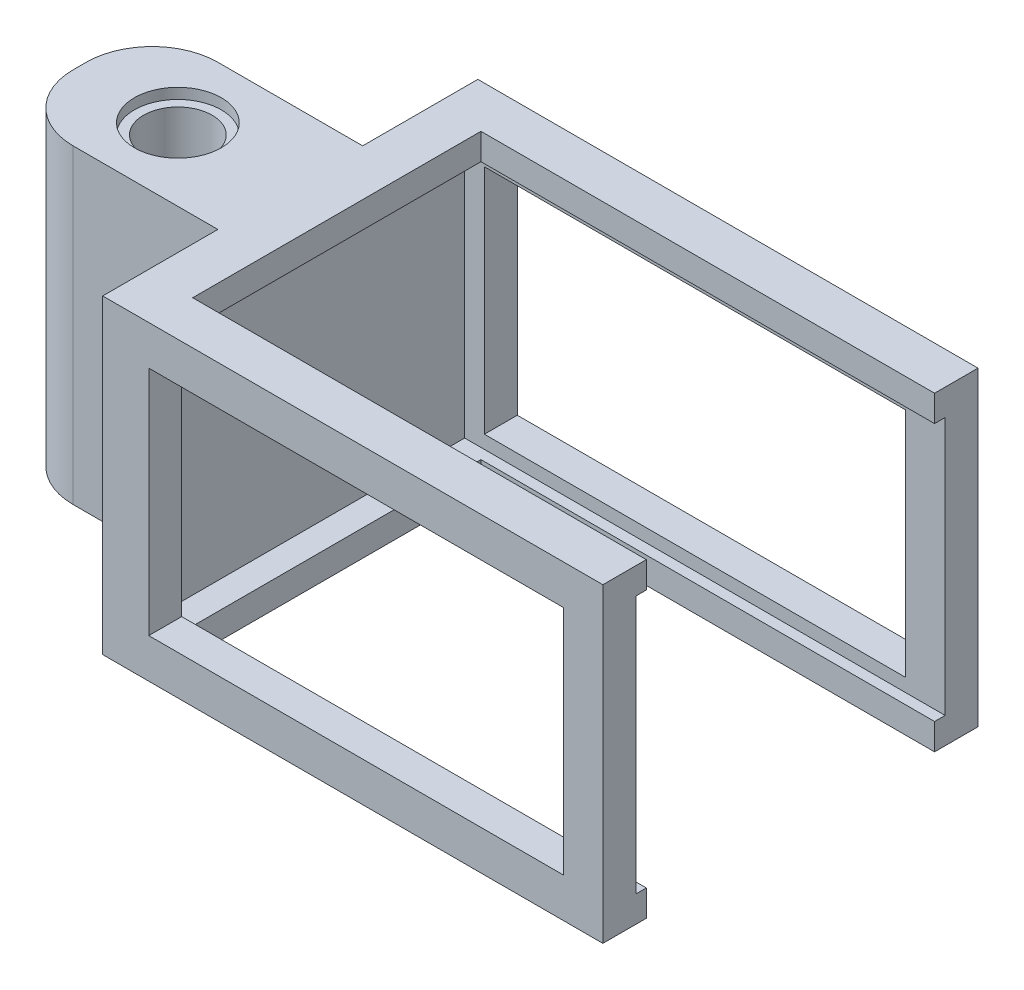
SolidWorks part; units mm, degrees
ref_plane "Front Plane" through (0, 0, 0) normal (0, 0, 1) x (1, 0, 0)
ref_plane "Top Plane" through (0, 0, 0) normal (0, 1, 0) x (1, 0, 0)
ref_plane "Right Plane" through (0, 0, 0) normal (1, 0, 0) x (0, 0, -1)
sketch "Sketch2" plane through (0, 0, 0) normal (0, 0, 1) x (1, 0, 0)
  line L1 (0, 0) -> (38, 0)
  line L2 (0, 0) -> (0, 23.6)
  line L3 (0, 23.6) -> (38, 23.6)
  line L4 (38, 0) -> (38, 23.6)
  dimension "D1" = 23.6
  dimension "D2" = 38
extrude "Boss-Extrude2" add sketch "Sketch2" along normal blind 2.5
sketch "Sketch3" plane through (0, 0, 2.5) normal (0, 0, 1) x (1, 0, 0)
  line L0 (38, 23.6) -> (38, 20.6) construction
  line L1 (38, 0) -> (38, 23.6) construction
  line L2 (38, 0) -> (38, 3) construction
  line L3 (0, 11.8) -> (3, 11.8) construction
  line L4 (0, 23.6) -> (0, 0) construction
  line L6 (38, 20.6) -> (3, 20.6)
  line L7 (38, 20.6) -> (38, 3)
  line L8 (38, 3) -> (3, 3)
  line L9 (3, 20.6) -> (3, 3)
  dimension "D1" = 3
  dimension "D2" = 3
  dimension "D3" = 3
extrude "Cut-Extrude2" cut sketch "Sketch3" against normal blind 2.5
sketch "Sketch5" plane through (0, 0, 2.5) normal (0, 0, 1) x (1, 0, 0)
  line L0 (38, 20.6) -> (38, 23.6) construction
  line L1 (0, 23.6) -> (38, 23.6)
  line L2 (0, 23.6) -> (0, 21.6)
  line L3 (0, 21.6) -> (38, 21.6)
  line L4 (38, 23.6) -> (38, 21.6)
  line L5 (0, 23.6) -> (0, 0) construction
  line L6 (38, 0) -> (0, 0)
  line L7 (38, 0) -> (38, 2)
  line L8 (38, 2) -> (0, 2)
  line L9 (0, 0) -> (0, 2)
  line L10 (0, 0) -> (1.5, 0) construction
  line L11 (0, 0) -> (1.5, 0)
  line L12 (0, 0) -> (0, 23.6)
  line L13 (0, 23.6) -> (1.5, 23.6)
  line L14 (1.5, 0) -> (1.5, 23.6)
  line L15 (0, 11.8) -> (1.5, 11.8) construction
  line M4 (38, 0) -> (38, 3)
  line M8 (38, 20.6) -> (38, 23.6)
  line M9 (38, 23.6) -> (0, 23.6)
  line M10 (0, 23.6) -> (0, 0)
  line M11 (0, 0) -> (38, 0)
  dimension "D1" = 2
  dimension "D2" = 2
  dimension "D3" = 1.5
extrude "Boss-Extrude3" add sketch "Sketch5" along normal blind 26 contours L14 L3 M8 M9 | L3 L14 L1 M10 | L8 L14 L3 M10 | L14 L8 M11 M10 | L14 L6 L8 M4
sketch "Sketch7" plane through (0, 2, 0) normal (0, 1, 0) x (1, 0, 0)
  line L0 (1.5, -28.5) -> (1.5, -2.5) construction
  line L1 (38, -28.5) -> (1.5, -28.5)
  line L2 (38, -28.5) -> (38, -26)
  line L3 (38, -26) -> (1.5, -26)
  line L4 (1.5, -28.5) -> (1.5, -26)
  dimension "D1" = 2.5
extrude "Boss-Extrude5" add sketch "Sketch7" along normal blind 1
sketch "Sketch10" plane through (0, 21.6, 0) normal (0, -1, 0) x (1, 0, 0)
  line L0 (38, 28.5) -> (38, 2.5) construction
  line L1 (1.5, 28.5) -> (38, 28.5)
  line L2 (1.5, 28.5) -> (1.5, 26)
  line L3 (1.5, 26) -> (38, 26)
  line L4 (38, 28.5) -> (38, 26)
  line L5 (25.4025, 26) -> (25.4025, 28.5)
  line M3 (38, 2.5) -> (38, 28.5)
  line M4 (38, 28.5) -> (1.5, 28.5)
  line M5 (1.5, 28.5) -> (1.5, 2.5)
  dimension "D1" = 2.5
extrude "Boss-Extrude6" add sketch "Sketch10" along normal blind 1 contours L5 L3 M3 M4 | L3 L5 L1 M5
sketch "Sketch11" plane through (1.5, 0, 0) normal (1, 0, 0) x (0, 0, -1)
  line L1 (-26, 3) -> (-28.5, 3)
  line L2 (-26, 3) -> (-26, 20.6)
  line L3 (-26, 20.6) -> (-28.5, 20.6)
  line L4 (-28.5, 3) -> (-28.5, 20.6)
extrude "Boss-Extrude7" add sketch "Sketch11" along normal blind 2
sketch "Sketch12" plane through (0, 21.6, 0) normal (0, -1, 0) x (-1, 0, 0)
  line L1 (12.2725, 16.9603) -> (-28.6118, 16.9603)
  line L2 (12.2725, 16.9603) -> (12.2725, 24.3169)
  line L3 (12.2725, 24.3169) -> (-28.6118, 24.3169)
  line L4 (-28.6118, 16.9603) -> (-28.6118, 24.3169)
ref_plane "Plane1" through (38, 21.6, 26) normal (0, 0, -1) x (-1, 0, 0)
sketch "Sketch15" plane through (0, 23.6, 0) normal (0, 1, 0) x (1, 0, 0)
  line L0 (34.1267, 0) -> (34.1267, -2.5) construction
  line L1 (38, 0) -> (0, 0) construction
  line L2 (34.5867, -28.5) -> (34.5867, -26) construction
  line L3 (38, -28.5) -> (0, -28.5) construction
  line L4 (44.4625, -26) -> (31.5375, -26) construction
  line L5 (0, -14.25) -> (3, -14.25) construction
  line L6 (0, -28.5) -> (0, 0) construction
  line L7 (38, -28.5) -> (38, 0) construction
  line L8 (34.1267, -2.5) -> (3.5372, -2.5)
  line L9 (34.1267, -2.5) -> (34.1267, -26)
  line L10 (34.1267, -26) -> (3.5372, -26)
  line L11 (3.5372, -2.5) -> (3.5372, -26)
  line L12 (3.5372, -2.5) -> (38, -2.5)
  line L13 (3.5372, -2.5) -> (3.5372, -26)
  line L14 (3.5372, -26) -> (38, -26)
  line L15 (38, -2.5) -> (38, -26)
  line M6 (38, -28.5) -> (38, 0)
  dimension "D1" = 2.5
  dimension "D2" = 3
extrude "Cut-Extrude4" cut sketch "Sketch15" against normal blind 30 contours L8 L11 L10 L9 | L9 L14 L12 M6
sketch "Sketch16" plane through (0, 3, 0) normal (0, 1, 0) x (1, 0, 0)
  line L0 (3, 0) -> (38, 0) construction
  line L1 (38, -2.5) -> (35, -2.5)
  line L2 (38, -2.5) -> (38, 0)
  line L3 (38, 0) -> (35, 0)
  line L4 (35, -2.5) -> (35, 0)
  dimension "D1" = 3
extrude "Boss-Extrude8" add sketch "Sketch16" along normal blind 20
sketch "Sketch17" plane through (0, 3, 0) normal (0, 1, 0) x (1, 0, 0)
  line L0 (38, -26) -> (3.5, -26) construction
  line L1 (38, -28.5) -> (35, -28.5)
  line L2 (38, -28.5) -> (38, -26)
  line L3 (38, -26) -> (35, -26)
  line L4 (35, -28.5) -> (35, -26)
  dimension "D1" = 3
extrude "Boss-Extrude9" add sketch "Sketch17" along normal blind 20
sketch "Sketch18" plane through (0, 23.6, 0) normal (0, 1, 0) x (1, 0, 0)
  line L0 (0, -14.25) -> (13.6, -14.25) construction
  line L1 (0, -28.5) -> (0, 0) construction
  circle A0 centre (13.6, -14.25) radius 3.69
  circle A1 centre (6.22, -14.25) radius 3.69
  circle A2 centre (-1.16, -14.25) radius 3.69
  circle A3 centre (-8.54, -14.25) radius 3.69
  dimension "D2" = 7.38
  dimension "D3" = 4
  dimension "D1" = 13.6
sketch "Sketch19" plane through (0, 0, 0) normal (-1, 0, 0) x (0, 0, 1)
  line L0 (28.5, 23.6) -> (0, 23.6) construction
  line L1 (14.25, 23.6) -> (8.75, 23.6)
  line L2 (14.25, 23.6) -> (14.25, 0)
  line L3 (14.25, 0) -> (8.75, 0)
  line L4 (8.75, 23.6) -> (8.75, 0)
  line L5 (28.5, 0) -> (0, 0) construction
  line L7 (14.25, 23.6) -> (19.75, 23.6)
  line L8 (14.25, 23.6) -> (14.25, 0)
  line L9 (14.25, 0) -> (19.75, 0)
  line L10 (19.75, 23.6) -> (19.75, 0)
  line M4 (0, 0) -> (28.5, 0)
  line M6 (28.5, 23.6) -> (0, 23.6)
  dimension "D1" = 5.5
  dimension "D2" = 5.5
extrude "Boss-Extrude10" add sketch "Sketch19" along normal blind 16 contours L10 L2 M6 M4 | L4 L2 M6 M4
sketch "Sketch20" plane through (0, 23.6, 0) normal (0, 1, 0) x (1, 0, 0)
  circle A0 centre (-8.54, -14.25) radius 2.6
  dimension "D1" = 5.2
extrude "Cut-Extrude6" cut sketch "Sketch20" against normal blind 30
sketch "Sketch21" plane through (0, 23.6, 0) normal (0, 1, 0) x (1, 0, 0)
  circle A0 centre (-8.54, -14.25) radius 3.3
  dimension "D1" = 6.6
extrude "Cut-Extrude7" cut sketch "Sketch21" against normal blind 0.8
sketch "Sketch22" plane through (0, 0, 0) normal (0, -1, 0) x (1, 0, 0)
  circle A0 centre (-8.54, 14.25) radius 3.3
  dimension "D1" = 6.6
extrude "Cut-Extrude8" cut sketch "Sketch22" against normal blind 0.8
fillet "Fillet1" radius 5 1 edges at (-16, 11.8, 8.75)
fillet "Fillet3" radius 5 1 edges at (-16, 11.8, 19.75)
sketch "Sketch23" plane through (0, 0, 26) normal (0, 0, -1) x (-1, 0, 0)
  line L1 (-3.5372, 21.6) -> (-38, 21.6)
  line L2 (-3.5372, 21.6) -> (-3.5372, 23.6)
  line L3 (-3.5372, 23.6) -> (-38, 23.6)
  line L4 (-38, 21.6) -> (-38, 23.6)
extrude "Boss-Extrude11" add sketch "Sketch23" along normal blind 0.8
sketch "Sketch24" plane through (0, 0, 2.5) normal (0, 0, 1) x (1, 0, 0)
  line L1 (3.5372, 21.6) -> (38, 21.6)
  line L2 (3.5372, 21.6) -> (3.5372, 23.6)
  line L3 (3.5372, 23.6) -> (38, 23.6)
  line L4 (38, 21.6) -> (38, 23.6)
extrude "Boss-Extrude12" add sketch "Sketch24" along normal blind 0.8
sketch "Sketch25" plane through (0, 0, 26) normal (0, 0, -1) x (-1, 0, 0)
  line L0 (-38, 21.6) -> (-38, 0) construction
  line L1 (-3.5372, 0) -> (-38, 0)
  line L2 (-3.5372, 0) -> (-3.5372, 2)
  line L3 (-3.5372, 2) -> (-38, 2)
  line L4 (-38, 0) -> (-38, 2)
  dimension "D1" = 2
extrude "Boss-Extrude13" add sketch "Sketch25" along normal blind 0.8
sketch "Sketch26" plane through (0, 0, 2.5) normal (0, 0, 1) x (1, 0, 0)
  line L0 (38, 0) -> (38, 21.6) construction
  line L1 (3.5372, 0) -> (38, 0)
  line L2 (3.5372, 0) -> (3.5372, 2)
  line L3 (3.5372, 2) -> (38, 2)
  line L4 (38, 0) -> (38, 2)
  dimension "D1" = 2
extrude "Boss-Extrude14" add sketch "Sketch26" along normal blind 0.8
